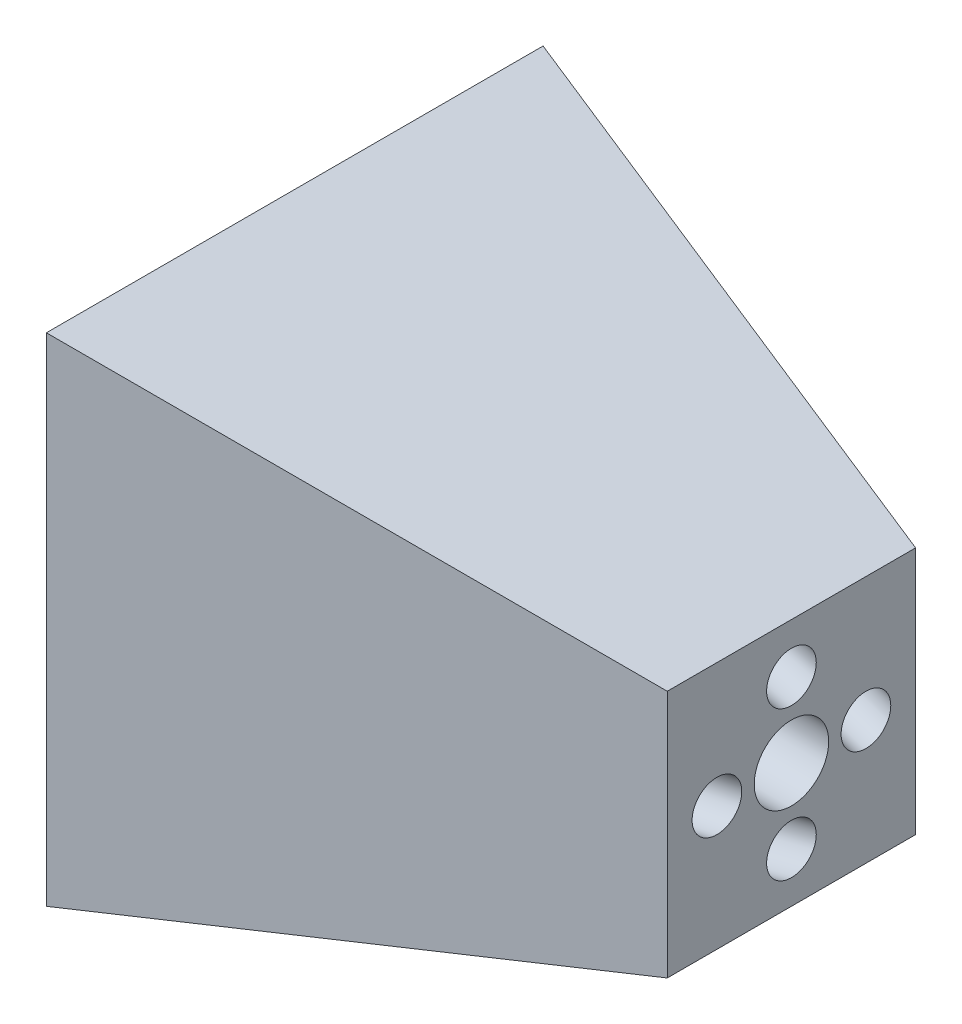
SolidWorks part; units mm, degrees
material "Pine"
ref_plane "Front Plane" through (0, 0, 0) normal (0, 0, 1) x (1, 0, 0)
ref_plane "Top Plane" through (0, 0, 0) normal (0, 1, 0) x (1, 0, 0)
ref_plane "Right Plane" through (0, 0, 0) normal (1, 0, 0) x (0, 0, -1)
other "Center of Mass"
sketch "Sketch1" plane through (0, 0, 0) normal (1, 0, 0) x (0, 0, -1)
  line L1 (25, 25) -> (-25, 25)
  line L2 (25, 25) -> (25, -25)
  line L3 (25, -25) -> (-25, -25)
  line L4 (-25, 25) -> (-25, -25)
  line L5 (25, 25) -> (-25, -25) construction
  line L6 (25, -25) -> (-25, 25) construction
  point P0 (0, 0)
  dimension "D1" = 50
ref_plane "Plane1" through (-100, 0, 0) normal (1, 0, 0) x (0, 0, -1)
sketch "Sketch2" plane through (-100, 0, 0) normal (1, 0, 0) x (0, 0, -1)
  line L1 (50, 50) -> (-50, 50)
  line L2 (50, 50) -> (50, -50)
  line L3 (50, -50) -> (-50, -50)
  line L4 (-50, 50) -> (-50, -50)
  line L5 (50, 50) -> (-50, -50) construction
  line L6 (50, -50) -> (-50, 50) construction
  point P0 (0, 0)
  dimension "D1" = 100
loft "Loft1" add profiles "Sketch1", "Sketch2"
sketch "Sketch3" plane through (0, 0, 0) normal (1, 0, 0) x (0, 0, -1)
  circle A0 centre (15, 0) radius 5
  circle A1 centre (0, -15) radius 5 construction
  circle A2 centre (-15, 0) radius 5 construction
  circle A3 centre (0, 15) radius 5 construction
  point P12 (0, 0)
  dimension "D1" = 10
  dimension "D2" = 15
  dimension "D3" = 4
sketch "Sketch4" plane through (0, 0, 0) normal (0, 1, 0) x (1, 0, 0)
  line L0 (0, 15) -> (-100, 40)
  line L1 (0, 10) -> (0, 20) construction
  line L2 (-100, 50) -> (-100, -50) construction
  line L3 (0, 25) -> (-100, 50) construction
  line L5 (0, 0) -> (-133.0226, 0) construction
  line L6 (0, -15) -> (-100, -40)
sketch "Sketch5" plane through (0, 0, 0) normal (0, 0, 1) x (1, 0, 0)
  line L0 (0, 15) -> (-100, 40)
  line L1 (0, 10) -> (0, 20) construction
  line L2 (-100, 50) -> (-100, -50) construction
  line L3 (0, 25) -> (-100, 50) construction
  line L4 (0, 0) -> (34.2438, 0) construction
  line L5 (0, -15) -> (-100, -40)
sweep "Cut-Sweep2" cut profiles "Sketch3" path "Sketch4"
sketch "Sketch6" plane through (0, 0, 0) normal (1, 0, 0) x (0, 0, -1)
  circle A0 centre (0, 15) radius 5 construction
  circle A1 centre (15, 0) radius 5
  circle A2 centre (15, 0) radius 5 construction
  circle A3 centre (0, 15) radius 5
  dimension "D1" = 0
sweep "Cut-Sweep3" cut profiles "Sketch6" path "Sketch5"
mirror "Mirror1" about plane through (0, 0, 0) normal (0, 0, 1) of "Cut-Sweep2"
mirror "Mirror2" about plane through (0, 0, 0) normal (0, 1, 0) of "Cut-Sweep3"
sketch "Sketch7" plane through (0, 0, 0) normal (1, 0, 0) x (0, 0, -1)
  circle A0 centre (0, 0) radius 7.5
  dimension "D1" = 15
extrude "Cut-Extrude1" cut sketch "Sketch7" against normal through all
